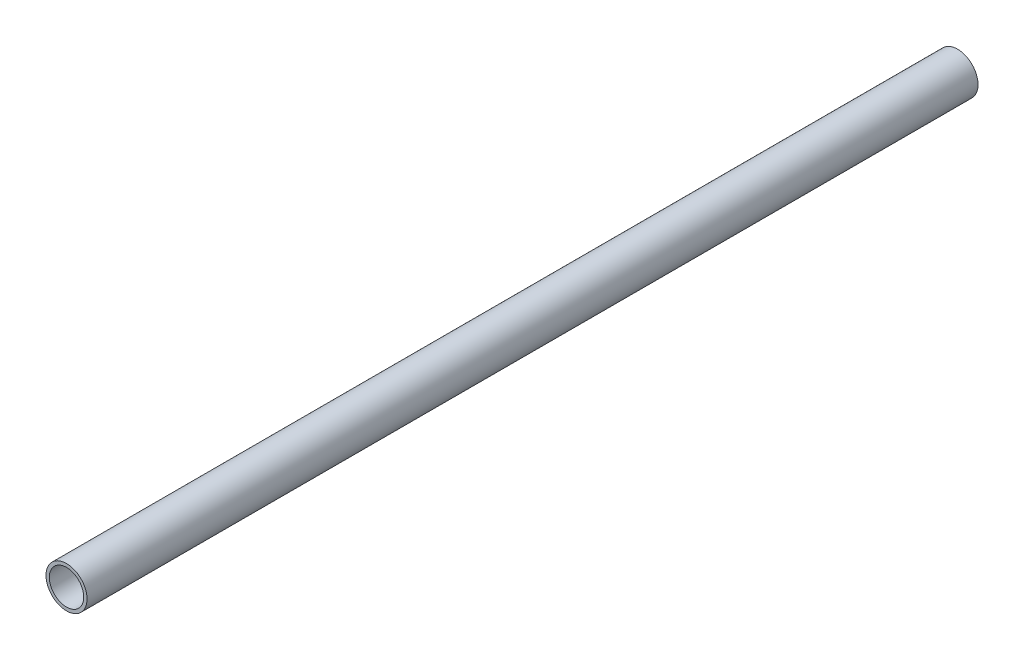
SolidWorks part; units mm, degrees
material "carbon"
ref_plane "Płaszczyzna XY" through (0, 0, 0) normal (0, 0, 1) x (1, 0, 0)
ref_plane "Płaszczyzna XZ" through (0, 0, 0) normal (0, 1, 0) x (1, 0, 0)
ref_plane "Płaszczyzna YZ" through (0, 0, 0) normal (1, 0, 0) x (0, 0, -1)
sketch "Szkic1" plane through (0, 0, 0) normal (0, 0, 1) x (1, 0, 0)
  circle A0 centre (0, 0) radius 7
  circle A1 centre (0, 0) radius 8.35
  dimension "D1" = 14
  dimension "D2" = 16.7
extrude "Dodanie-wyciągnięcie1" add sketch "Szkic1" along normal up to surface (337.5704 mm away) and the other way up to surface (25 mm away)
